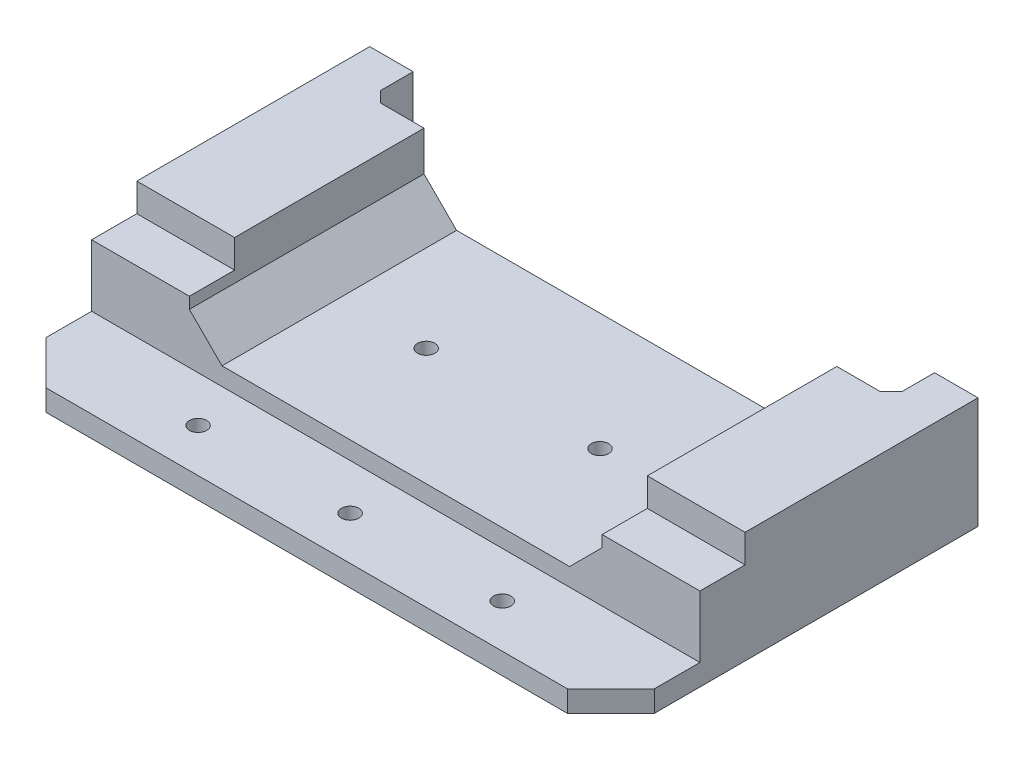
SolidWorks part; units mm, degrees
material "PET"
ref_plane "Front" through (0, 0, 0) normal (0, 0, 1) x (1, 0, 0)
ref_plane "Top" through (0, 0, 0) normal (0, 1, 0) x (1, 0, 0)
ref_plane "Right" through (0, 0, 0) normal (1, 0, 0) x (0, 0, -1)
sketch "Sketch1" plane through (0, 0, 0) normal (0, 0, 1) x (1, 0, 0)
  line L8 (-88.9, 42.038) -> (88.9, 42.038)
  line L9 (88.9, 42.038) -> (88.9, 77.7875)
  line L10 (88.9, 77.7875) -> (-88.9, 77.7875)
  line L11 (-88.9, 77.7875) -> (-88.9, 42.038)
extrude "Boss-Extrude1" add sketch "Sketch1" along normal up to surface (15.24 mm away)
sketch "Sketch2" plane through (0, 42.038, 0) normal (0, -1, 0) x (1, 0, 0)
  line L0 (-117.9738, 41.275) -> (-246.8337, 41.275) construction
  line L1 (88.9, -66.04) -> (-88.9, -66.04)
  line L2 (88.9, -66.04) -> (88.9, 41.275)
  line L3 (88.9, 41.275) -> (-88.9, 41.275)
  line L4 (-88.9, -66.04) -> (-88.9, 41.275)
extrude "Boss-Extrude2" add sketch "Sketch2" against normal up to surface (6.222 mm away)
chamfer "Chamfer1" distance 12.7 angle 45 2 edges at (-88.9, 45.149, 41.275) (88.9, 45.149, 41.275)
hole_wizard "#8 (0.199) Diameter Hole2" positions "Sketch5" profile "Sketch6" hole size "#8" standard "ANSI Inch" end condition through all
sketch "Sketch5" plane through (0, 42.038, 0) normal (0, -1, 0) x (-1, 0, 0)
  line L3 (88.9, -28.575) -> (0, -28.575) construction
  line L4 (88.9, -28.575) -> (88.9, 66.04) construction
  line L5 (88.9, 0) -> (-88.9, 0) construction
  line L9 (-76.2, -41.275) -> (76.2, -41.275) construction
  line L10 (0, -28.575) -> (-88.9, -28.575) construction
  line L12 (-88.9, -28.575) -> (-88.9, 66.04) construction
  point P8 (0, -28.575)
  point P21 (44.45, -28.575)
  point P31 (0, 0)
  point P48 (-44.45, -28.575)
  dimension "D1" = 12.7
sketch "Sketch6" plane through (44.45, 42.038, 28.575) normal (1, 0, 0) x (0, 0, -1)
  line L0 (0, 0) -> (0, 35.7495)
  line L1 (0, 35.7495) -> (2.5273, 35.7495)
  line L2 (2.5273, 35.7495) -> (2.5273, 0)
  line L5 (2.5273, 0) -> (0, 0)
  line L11 (0, -6.35) -> (0, 107.95) construction
  dimension "Thru Hole Dia." = 5.0546
  dimension "Thru Hole Depth" = 35.7495
sketch "Sketch7" plane through (0, 0, 15.24) normal (0, 0, 1) x (1, 0, 0)
  line L0 (0, 48.26) -> (0, 77.7875) construction
  line L1 (-88.9, 48.26) -> (88.9, 48.26) construction
  line L2 (88.9, 77.7875) -> (-88.9, 77.7875) construction
  line L3 (-50.8, 63.0237) -> (50.8, 63.0237) construction
  line L4 (-50.8, 72.5487) -> (50.8, 72.5487)
  line L6 (-50.8, 53.4987) -> (50.8, 53.4987)
  arc A4 (-50.8, 72.5487) -> (-50.8, 53.4987) centre (-50.8, 63.0237) ccw
  arc A5 (50.8, 53.4987) -> (50.8, 72.5487) centre (50.8, 63.0237) ccw
  point P8 (0, 63.0237)
  dimension "D1" = 9.525
  dimension "D2" = 101.6
extrude "Cut-Extrude1" cut sketch "Sketch7" against normal through all
sketch "Sketch8" plane through (0, 0, 0) normal (0, 0, -1) x (-1, 0, 0)
  line L2 (50.8, 72.5487) -> (-50.8, 72.5487)
  line L3 (-50.8, 53.4987) -> (50.8, 53.4987)
  line L4 (-88.9, 48.26) -> (88.9, 48.26)
  line L5 (88.9, 48.26) -> (88.9, 77.7875)
  line L6 (88.9, 77.7875) -> (-88.9, 77.7875)
  line L7 (-88.9, 77.7875) -> (-88.9, 48.26)
  line L8 (-88.9, 48.26) -> (88.9, 48.26)
  line L9 (88.9, 48.26) -> (88.9, 77.7875)
  line L10 (88.9, 77.7875) -> (-88.9, 77.7875)
  line L11 (-88.9, 77.7875) -> (-88.9, 48.26)
  line L12 (50.8, 72.5487) -> (-50.8, 72.5487)
  line L13 (-50.8, 53.4987) -> (50.8, 53.4987)
  arc A2 (50.8, 53.4987) -> (50.8, 72.5487) centre (50.8, 63.0237) ccw
  arc A3 (-50.8, 72.5487) -> (-50.8, 53.4987) centre (-50.8, 63.0237) ccw
  arc A4 (50.8, 53.4987) -> (50.8, 72.5487) centre (50.8, 63.0237) ccw
  arc A5 (-50.8, 72.5487) -> (-50.8, 53.4987) centre (-50.8, 63.0237) ccw
  dimension "D1" = 0
  dimension "D2" = 0
extrude "Boss-Extrude3" add sketch "Sketch8" along normal up to surface (66.04 mm away) up to face at (0, 45.149, -66.04)
sketch "Sketch9" plane through (0, 42.038, 0) normal (0, -1, 0) x (1, 0, 0)
  line L0 (-88.9, -66.04) -> (88.9, -66.04) construction
  line L1 (76.2, -66.04) -> (-76.2, -66.04)
  line L2 (76.2, -66.04) -> (76.2, -53.34)
  line L3 (76.2, -53.34) -> (-76.2, -53.34)
  line L4 (-76.2, -66.04) -> (-76.2, -53.34)
  dimension "D1" = 76.2
  dimension "D2" = 76.2
  dimension "D3" = 12.7
extrude "Cut-Extrude2" cut sketch "Sketch9" against normal through all
sketch "Sketch10" plane through (0, 0, -66.04) normal (0, 0, -1) x (-1, 0, 0)
  line L0 (-88.9, 77.7875) -> (-88.9, 42.038) construction
  line L1 (88.9, 77.7875) -> (-88.9, 77.7875)
  line L2 (88.9, 77.7875) -> (88.9, 74.6125)
  line L3 (88.9, 74.6125) -> (-88.9, 74.6125)
  line L4 (-88.9, 77.7875) -> (-88.9, 74.6125)
  dimension "D1" = 3.175
extrude "Cut-Extrude3" cut sketch "Sketch10" against normal through all
sketch "Sketch11" plane through (88.9, 0, 0) normal (1, 0, 0) x (0, 0, -1)
  line L0 (-15.24, 74.6125) -> (66.04, 74.6125) construction
  line L1 (-2.032, 74.6125) -> (-15.24, 74.6125)
  line L2 (-2.032, 74.6125) -> (-2.032, 66.3575)
  line L3 (-2.032, 66.3575) -> (-15.24, 66.3575)
  line L4 (-15.24, 74.6125) -> (-15.24, 66.3575)
  line L5 (-15.24, 48.26) -> (-15.24, 74.6125) construction
  dimension "D1" = 13.208
  dimension "D2" = 8.255
extrude "Cut-Extrude4" cut sketch "Sketch11" against normal through all
sketch "Sketch12" plane through (0, 0, -53.34) normal (0, 0, -1) x (-1, 0, 0)
  line L0 (76.2, 74.6125) -> (-76.2, 74.6125) construction
  line L1 (-60.325, 63.0237) -> (60.325, 63.0237)
  line L2 (-60.325, 63.0237) -> (-60.325, 74.6125)
  line L3 (-60.325, 74.6125) -> (60.325, 74.6125)
  line L4 (60.325, 63.0237) -> (60.325, 74.6125)
  arc A0 (-50.8, 72.5487) -> (-50.8, 53.4987) centre (-50.8, 63.0237) ccw construction
  arc A1 (50.8, 53.4987) -> (50.8, 72.5487) centre (50.8, 63.0237) ccw construction
extrude "Cut-Extrude5" cut sketch "Sketch12" against normal through all
sketch "Sketch13" plane through (0, 0, 15.24) normal (0, 0, 1) x (1, 0, 0)
  line L0 (60.325, 63.0237) -> (50.8, 53.4987)
  line L1 (-60.325, 63.0237) -> (-50.8, 53.4987)
  arc A0 (50.8, 53.4987) -> (60.325, 63.0237) centre (50.8, 63.0237) ccw construction
  arc A1 (50.8, 53.4987) -> (60.325, 63.0237) centre (50.8, 63.0237) ccw
  arc A2 (-60.325, 63.0237) -> (-50.8, 53.4987) centre (-50.8, 63.0237) ccw construction
  arc A3 (-60.325, 63.0237) -> (-50.8, 53.4987) centre (-50.8, 63.0237) ccw
extrude "Boss-Extrude4" add sketch "Sketch13" against normal up to surface (68.58 mm away) up to face at (0, 61.1626, -53.34)
chamfer "Chamfer2" distance 3.175 angle 45 2 edges at (76.2, 58.3252, -53.34) (-76.2, 58.3252, -53.34)
hole_wizard "#8 (0.199) Diameter Hole1" positions "Sketch21" profile "Sketch3" hole size "#8" standard "ANSI Inch" end condition up to next
sketch "Sketch21" plane through (9.8846, 42.038, -19.495) normal (0, -1, 0) x (-1, 0, 0)
  point P0 (-15.5154, -0.445)
  point P3 (35.2846, -0.445)
sketch "Sketch3" plane through (25.4, 42.038, -19.05) normal (1, 0, 0) x (0, 0, -1)
  line L0 (0, 0) -> (0, 11.4608)
  line L1 (0, 11.4608) -> (2.5273, 11.4608)
  line L2 (2.5273, 11.4608) -> (2.5273, 0)
  line L5 (2.5273, 0) -> (0, 0)
  line L11 (0, -6.35) -> (0, 107.95) construction
  dimension "Thru Hole Dia." = 5.0546
  dimension "Thru Hole Depth" = 11.4608
hole_wizard "#8 Plastic Insert" positions "Sketch4" profile "Sketch51" legacy
sketch "Sketch4" plane through (9.8846, 42.038, -19.495) normal (0, -1, 0) x (-1, 0, 0)
  point P0 (-15.5154, -0.445)
  point P3 (35.2846, -0.445)
sketch "Sketch51" plane through (25.4, 42.038, -19.05) normal (1, 0, 0) x (0, 0, -1)
  line L0 (0, 0) -> (0, 4.699)
  line L1 (0, 4.699) -> (2.8702, 4.699)
  line L2 (2.8702, 4.699) -> (2.9972, 0)
  line L3 (2.9972, 0) -> (0, 0)
  line L4 (0, 110) -> (0, -10) construction
  dimension "Minor Diameter" = 5.7404
  dimension "Depth" = 4.699
  dimension "Major Diameter" = 5.9944
other "#8 Plastic Insert Hole<1>"
